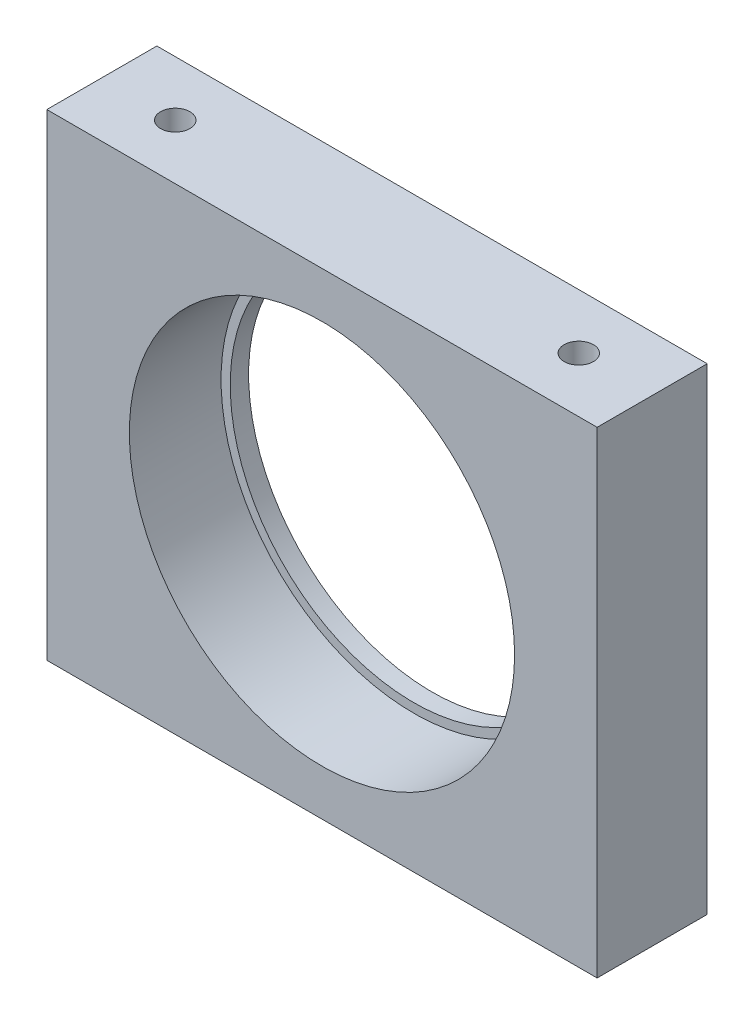
SolidWorks part; units mm, degrees
material "Alliage 1060"
ref_plane "Plan de face" through (0, 0, 0) normal (0, 0, 1) x (1, 0, 0)
ref_plane "Plan de dessus" through (0, 0, 0) normal (0, 1, 0) x (1, 0, 0)
ref_plane "Plan de droite" through (0, 0, 0) normal (1, 0, 0) x (0, 0, -1)
sketch "Esquisse1" plane through (0, 0, 0) normal (0, 0, 1) x (1, 0, 0)
  line L1 (0, 0) -> (30, 0)
  line L2 (0, 0) -> (0, 26)
  line L3 (0, 26) -> (30, 26)
  line L4 (30, 0) -> (30, 26)
  circle A0 centre (15, 13) radius 10
  dimension "D3" = 20
  dimension "D1" = 30
  dimension "D2" = 26
  dimension "D4" = 15
  dimension "D5" = 13
extrude "Boss.-Extru.1" add sketch "Esquisse1" along normal blind 6
sketch "Esquisse2" plane through (0, 0, 6) normal (0, 0, 1) x (1, 0, 0)
  line L0 (30, 26) -> (0, 26) construction
  line L2 (30, 0) -> (30, 26) construction
  circle A0 centre (15, 13) radius 10.5
  dimension "D3" = 21
  dimension "D1" = 13
  dimension "D2" = 15
extrude "Enlèv. mat.-Extru.1" cut sketch "Esquisse2" against normal blind 5
hole_wizard "Trou pour taraudage pour trou taraudé M21" positions "Esquisse3" profile "Esquisse4" hole size "M2" standard "ISO"
sketch "Esquisse3" plane through (0, 26, 0) normal (0, 1, 0) x (1, 0, 0)
  line L0 (0, -6) -> (0, 0) construction
  line L1 (30, -6) -> (30, 0) construction
  line L2 (30, -6) -> (0, -6) construction
  point P0 (4, -3)
  point P2 (26, -3)
  dimension "D1" = 4
  dimension "D2" = 4
  dimension "D3" = 3
  dimension "D4" = 3
sketch "Esquisse4" plane through (4, 26, 3) normal (1, 0, 0) x (0, 0, 1)
  line L0 (0, 0) -> (0, 10.4807)
  line L1 (0, 10.4807) -> (0.8, 10)
  line L2 (0.8, 10) -> (0.8, 0)
  line L5 (0.8, 0) -> (0, 0)
  line L10 (0, 10.4807) -> (-0.8, 10) construction
  line L11 (0, -6.35) -> (0, 107.95) construction
  dimension "Diamètre du perçage" = 1.6
  dimension "Profondeur du perçage" = 10
  dimension "Angle de pointe" = 118
hole_wizard "Trou pour taraudage pour trou taraudé M22" positions "Esquisse5" profile "Esquisse6" hole size "M2" standard "ISO"
sketch "Esquisse5" plane through (0, 0, 0) normal (0, -1, 0) x (-1, 0, 0)
  line L0 (0, 0) -> (-30, 0) construction
  line L1 (0, -6) -> (0, 0) construction
  line L2 (-30, -6) -> (-30, 0) construction
  point P0 (-26, -3)
  point P2 (-4, -3)
  dimension "D2" = 3
  dimension "D3" = 4
  dimension "D4" = 4
sketch "Esquisse6" plane through (26, 0, 3) normal (1, 0, 0) x (0, 0, -1)
  line L0 (0, 0) -> (0, 10.4807)
  line L1 (0, 10.4807) -> (0.8, 10)
  line L2 (0.8, 10) -> (0.8, 0)
  line L5 (0.8, 0) -> (0, 0)
  line L10 (0, 10.4807) -> (-0.8, 10) construction
  line L11 (0, -6.35) -> (0, 107.95) construction
  dimension "Diamètre du perçage" = 1.6
  dimension "Profondeur du perçage" = 10
  dimension "Angle de pointe" = 118
equation "\"D4@Esquisse1\"=\"D1@Esquisse1\"/2"
equation "\"D5@Esquisse1\"=\"D2@Esquisse1\"/2"
equation "\"D1@Esquisse2\"=\"D2@Esquisse1\"/2"
equation "\"D2@Esquisse2\"=\"D1@Esquisse1\"/2"
equation "\"D3@Esquisse3\"=\"D1@Boss.-Extru.1\"/2"
equation "\"D4@Esquisse3\"=\"D3@Esquisse3\""
equation "\"D1@Esquisse5\"=\"D1@Boss.-Extru.1\"/2"
equation "\"D2@Esquisse5\"=\"D1@Boss.-Extru.1\"/2"
